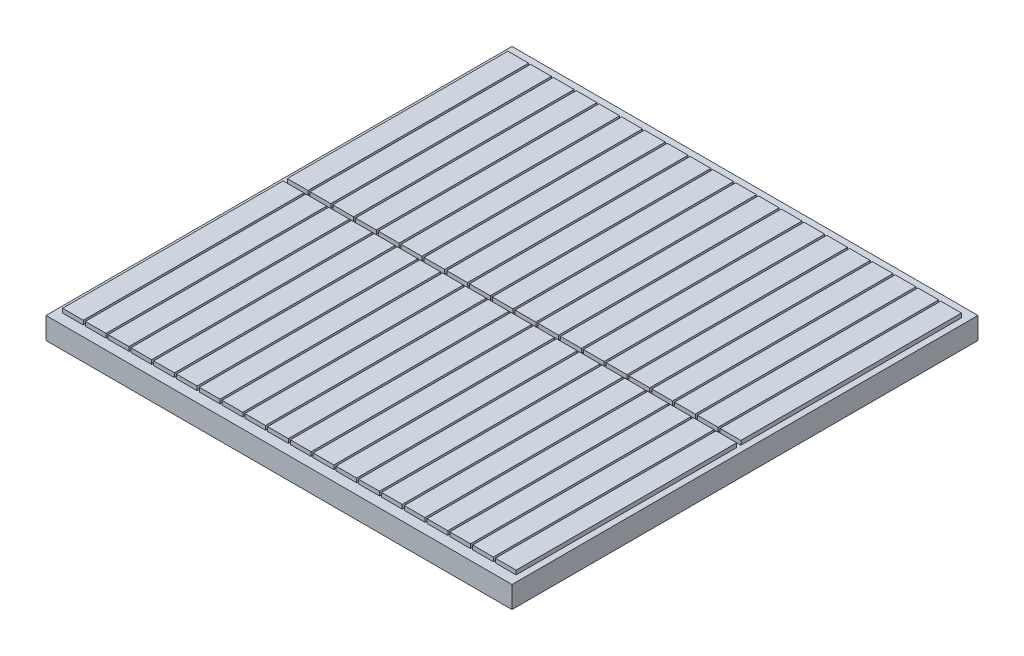
SolidWorks part; units mm, degrees
ref_plane "Front Plane" through (0, 0, 0) normal (0, 0, 1) x (1, 0, 0)
ref_plane "Top Plane" through (0, 0, 0) normal (0, 1, 0) x (1, 0, 0)
ref_plane "Right Plane" through (0, 0, 0) normal (1, 0, 0) x (0, 0, -1)
sketch "Sketch1" plane through (0, 0, 0) normal (0, 1, 0) x (1, 0, 0)
  line L5 (-22.5, 22.5) -> (22.5, 22.5)
  line L6 (-22.5, 22.5) -> (-22.5, -22.5)
  line L7 (-22.5, -22.5) -> (22.5, -22.5)
  line L8 (22.5, 22.5) -> (22.5, -22.5)
  line L9 (-22.5, 22.5) -> (22.5, -22.5) construction
  line L10 (-22.5, -22.5) -> (22.5, 22.5) construction
  point P0 (0, 0)
  point P1 (0, 0)
  dimension "D1" = 45
  dimension "D2" = 45
extrude "Boss-Extrude1" add sketch "Sketch1" along normal blind 0.1
sketch "Sketch2" plane through (0, 0.1, 0) normal (0, 1, 0) x (1, 0, 0)
  line L1 (-22.5, 22.5) -> (22.5, 22.5)
  line L2 (-22.5, 22.5) -> (-22.5, -22.5)
  line L3 (-22.5, -22.5) -> (22.5, -22.5)
  line L4 (22.5, 22.5) -> (22.5, -22.5)
  line L5 (-22.5, 22.5) -> (22.5, -22.5) construction
  line L6 (-22.5, -22.5) -> (22.5, 22.5) construction
  point P0 (0, 0)
  dimension "D1" = 45
  dimension "D2" = 45
extrude "Boss-Extrude2" add sketch "Sketch2" along normal blind 2
sketch "Sketch5" plane through (0, 2.1, 0) normal (0, 1, 0) x (1, 0, 0)
  line L0 (22.5, 22.5) -> (-22.5, 22.5) construction
  line L1 (-21.9, 21.5) -> (-19.9, 21.5)
  line L2 (-21.9, 21.5) -> (-21.9, 0.2)
  line L3 (-21.9, 0.2) -> (-19.9, 0.2)
  line L4 (-19.9, 21.5) -> (-19.9, 0.2)
  line L5 (-22.5, 22.5) -> (-22.5, -22.5) construction
  line L6 (-19.7, 21.5) -> (-19.7, 0.2)
  line L7 (-19.7, 21.5) -> (-17.7, 21.5)
  line L56 (-21.9, 21.5) -> (-19.7, 21.5) construction
  line L57 (-17.7, 21.5) -> (-17.7, 0.2)
  line L110 (-19.7, 0.2) -> (-17.7, 0.2)
  line L111 (-17.5, 21.5) -> (-17.5, 0.2)
  line L112 (-17.5, 21.5) -> (-15.5, 21.5)
  line L113 (-15.5, 21.5) -> (-15.5, 0.2)
  line L114 (-17.5, 0.2) -> (-15.5, 0.2)
  line L115 (-15.3, 21.5) -> (-15.3, 0.2)
  line L116 (-15.3, 21.5) -> (-13.3, 21.5)
  line L117 (-13.3, 21.5) -> (-13.3, 0.2)
  line L118 (-15.3, 0.2) -> (-13.3, 0.2)
  line L119 (-13.1, 21.5) -> (-13.1, 0.2)
  line L120 (-13.1, 21.5) -> (-11.1, 21.5)
  line L121 (-11.1, 21.5) -> (-11.1, 0.2)
  line L122 (-13.1, 0.2) -> (-11.1, 0.2)
  line L123 (-10.9, 21.5) -> (-10.9, 0.2)
  line L124 (-10.9, 21.5) -> (-8.9, 21.5)
  line L125 (-8.9, 21.5) -> (-8.9, 0.2)
  line L126 (-10.9, 0.2) -> (-8.9, 0.2)
  line L127 (-8.7, 21.5) -> (-8.7, 0.2)
  line L128 (-8.7, 21.5) -> (-6.7, 21.5)
  line L129 (-6.7, 21.5) -> (-6.7, 0.2)
  line L130 (-8.7, 0.2) -> (-6.7, 0.2)
  line L131 (-6.5, 21.5) -> (-6.5, 0.2)
  line L132 (-6.5, 21.5) -> (-4.5, 21.5)
  line L133 (-4.5, 21.5) -> (-4.5, 0.2)
  line L134 (-6.5, 0.2) -> (-4.5, 0.2)
  line L135 (-4.3, 21.5) -> (-4.3, 0.2)
  line L136 (-4.3, 21.5) -> (-2.3, 21.5)
  line L137 (-2.3, 21.5) -> (-2.3, 0.2)
  line L138 (-4.3, 0.2) -> (-2.3, 0.2)
  line L139 (-2.1, 21.5) -> (-2.1, 0.2)
  line L140 (-2.1, 21.5) -> (-0.1, 21.5)
  line L141 (-0.1, 21.5) -> (-0.1, 0.2)
  line L142 (-2.1, 0.2) -> (-0.1, 0.2)
  line L143 (0.1, 21.5) -> (0.1, 0.2)
  line L144 (0.1, 21.5) -> (2.1, 21.5)
  line L145 (2.1, 21.5) -> (2.1, 0.2)
  line L146 (0.1, 0.2) -> (2.1, 0.2)
  line L147 (2.3, 21.5) -> (2.3, 0.2)
  line L148 (2.3, 21.5) -> (4.3, 21.5)
  line L149 (4.3, 21.5) -> (4.3, 0.2)
  line L150 (2.3, 0.2) -> (4.3, 0.2)
  line L151 (4.5, 21.5) -> (4.5, 0.2)
  line L152 (4.5, 21.5) -> (6.5, 21.5)
  line L153 (6.5, 21.5) -> (6.5, 0.2)
  line L154 (4.5, 0.2) -> (6.5, 0.2)
  line L155 (6.7, 21.5) -> (6.7, 0.2)
  line L156 (6.7, 21.5) -> (8.7, 21.5)
  line L157 (8.7, 21.5) -> (8.7, 0.2)
  line L158 (6.7, 0.2) -> (8.7, 0.2)
  line L159 (8.9, 21.5) -> (8.9, 0.2)
  line L160 (8.9, 21.5) -> (10.9, 21.5)
  line L161 (10.9, 21.5) -> (10.9, 0.2)
  line L162 (8.9, 0.2) -> (10.9, 0.2)
  line L163 (11.1, 21.5) -> (11.1, 0.2)
  line L164 (11.1, 21.5) -> (13.1, 21.5)
  line L165 (13.1, 21.5) -> (13.1, 0.2)
  line L166 (11.1, 0.2) -> (13.1, 0.2)
  line L167 (13.3, 21.5) -> (13.3, 0.2)
  line L168 (13.3, 21.5) -> (15.3, 21.5)
  line L169 (15.3, 21.5) -> (15.3, 0.2)
  line L170 (13.3, 0.2) -> (15.3, 0.2)
  line L171 (15.5, 21.5) -> (15.5, 0.2)
  line L172 (15.5, 21.5) -> (17.5, 21.5)
  line L173 (17.5, 21.5) -> (17.5, 0.2)
  line L174 (15.5, 0.2) -> (17.5, 0.2)
  line L175 (17.7, 21.5) -> (17.7, 0.2)
  line L176 (17.7, 21.5) -> (19.7, 21.5)
  line L177 (19.7, 21.5) -> (19.7, 0.2)
  line L178 (17.7, 0.2) -> (19.7, 0.2)
  line L179 (19.9, 21.5) -> (19.9, 0.2)
  line L180 (19.9, 21.5) -> (21.9, 21.5)
  line L181 (21.9, 21.5) -> (21.9, 0.2)
  line L182 (19.9, 0.2) -> (21.9, 0.2)
  line L184 (0, 0) -> (0.7148, 0)
  line L185 (-17.5, -21.5) -> (-15.5, -21.5)
  line L186 (-19.7, -21.5) -> (-17.7, -21.5)
  line L187 (-21.9, -21.5) -> (-19.9, -21.5)
  line L188 (-15.3, -21.5) -> (-13.3, -21.5)
  line L189 (-13.1, -21.5) -> (-11.1, -21.5)
  line L190 (2.3, -21.5) -> (4.3, -21.5)
  line L191 (0.1, -21.5) -> (2.1, -21.5)
  line L192 (-2.1, -21.5) -> (-0.1, -21.5)
  line L193 (-4.3, -21.5) -> (-2.3, -21.5)
  line L194 (-6.5, -21.5) -> (-4.5, -21.5)
  line L195 (-8.7, -21.5) -> (-6.7, -21.5)
  line L196 (-10.9, -21.5) -> (-8.9, -21.5)
  line L197 (4.5, -21.5) -> (6.5, -21.5)
  line L198 (6.7, -21.5) -> (8.7, -21.5)
  line L199 (8.9, -21.5) -> (10.9, -21.5)
  line L200 (11.1, -21.5) -> (13.1, -21.5)
  line L201 (15.5, -21.5) -> (17.5, -21.5)
  line L202 (13.3, -21.5) -> (15.3, -21.5)
  line L203 (19.9, -21.5) -> (21.9, -21.5)
  line L204 (17.7, -21.5) -> (19.7, -21.5)
  line L205 (19.9, -0.2) -> (21.9, -0.2)
  line L206 (17.7, -0.2) -> (19.7, -0.2)
  line L207 (15.5, -0.2) -> (17.5, -0.2)
  line L208 (13.3, -0.2) -> (15.3, -0.2)
  line L209 (11.1, -0.2) -> (13.1, -0.2)
  line L210 (10.9, -21.5) -> (10.9, -0.2)
  line L211 (11.1, -21.5) -> (11.1, -0.2)
  line L212 (13.3, -21.5) -> (13.3, -0.2)
  line L213 (13.1, -21.5) -> (13.1, -0.2)
  line L214 (15.3, -21.5) -> (15.3, -0.2)
  line L215 (15.5, -21.5) -> (15.5, -0.2)
  line L216 (17.5, -21.5) -> (17.5, -0.2)
  line L217 (17.7, -21.5) -> (17.7, -0.2)
  line L218 (19.7, -21.5) -> (19.7, -0.2)
  line L219 (19.9, -21.5) -> (19.9, -0.2)
  line L220 (21.9, -21.5) -> (21.9, -0.2)
  line L221 (8.7, -21.5) -> (8.7, -0.2)
  line L222 (8.9, -21.5) -> (8.9, -0.2)
  line L223 (8.9, -0.2) -> (10.9, -0.2)
  line L224 (6.7, -0.2) -> (8.7, -0.2)
  line L225 (4.5, -0.2) -> (6.5, -0.2)
  line L226 (2.3, -0.2) -> (4.3, -0.2)
  line L227 (0.1, -0.2) -> (2.1, -0.2)
  line L228 (-2.1, -0.2) -> (-0.1, -0.2)
  line L229 (-2.3, -21.5) -> (-2.3, -0.2)
  line L230 (-2.1, -21.5) -> (-2.1, -0.2)
  line L231 (-0.1, -21.5) -> (-0.1, -0.2)
  line L232 (0.1, -21.5) -> (0.1, -0.2)
  line L233 (2.1, -21.5) -> (2.1, -0.2)
  line L234 (2.3, -21.5) -> (2.3, -0.2)
  line L235 (4.3, -21.5) -> (4.3, -0.2)
  line L236 (4.5, -21.5) -> (4.5, -0.2)
  line L237 (6.5, -21.5) -> (6.5, -0.2)
  line L238 (6.7, -21.5) -> (6.7, -0.2)
  line L239 (-4.3, -0.2) -> (-2.3, -0.2)
  line L240 (-4.3, -21.5) -> (-4.3, -0.2)
  line L241 (-4.5, -21.5) -> (-4.5, -0.2)
  line L242 (-6.5, -0.2) -> (-4.5, -0.2)
  line L243 (-6.5, -21.5) -> (-6.5, -0.2)
  line L244 (-6.7, -21.5) -> (-6.7, -0.2)
  line L245 (-8.7, -21.5) -> (-8.7, -0.2)
  line L246 (-8.9, -21.5) -> (-8.9, -0.2)
  line L247 (-17.7, -21.5) -> (-17.7, -0.2)
  line L248 (-17.5, -21.5) -> (-17.5, -0.2)
  line L249 (-15.5, -21.5) -> (-15.5, -0.2)
  line L250 (-15.3, -21.5) -> (-15.3, -0.2)
  line L251 (-13.1, -21.5) -> (-13.1, -0.2)
  line L252 (-13.3, -21.5) -> (-13.3, -0.2)
  line L253 (-10.9, -21.5) -> (-10.9, -0.2)
  line L254 (-11.1, -21.5) -> (-11.1, -0.2)
  line L255 (-8.7, -0.2) -> (-6.7, -0.2)
  line L256 (-10.9, -0.2) -> (-8.9, -0.2)
  line L257 (-13.1, -0.2) -> (-11.1, -0.2)
  line L258 (-15.3, -0.2) -> (-13.3, -0.2)
  line L259 (-17.5, -0.2) -> (-15.5, -0.2)
  line L260 (-19.7, -0.2) -> (-17.7, -0.2)
  line L261 (-19.7, -21.5) -> (-19.7, -0.2)
  line L262 (-19.9, -21.5) -> (-19.9, -0.2)
  line L263 (-21.9, -0.2) -> (-19.9, -0.2)
  line L264 (-21.9, -21.5) -> (-21.9, -0.2)
  dimension "D1" = 1
  dimension "D2" = 0.6
  dimension "D3" = 2
  dimension "D4" = 20
extrude "Boss-Extrude3" add sketch "Sketch5" along normal blind 0.4 contours L4 L1 L2 L3 | L6 L110 L57 L7 | L111 L114 L113 L112 | L115 L118 L117 L116 | L119 L122 L121 L120 | L123 L126 L125 L124 | L127 L130 L129 L128 | L131 L134 L133 L132 | L135 L138 L137 L136 | L139 L142 L141 L140 | L143 L146 L145 L144 | L147 L150 L149 L148 | L155 L158 L157 L156 | L159 L162 L161 L160 | L163 L166 L165 L164 | L167 L170 L169 L168 | L171 L174 L173 L172 | L175 L178 L177 L176 | L179 L182 L181 L180 | L203 L220 L205 L219 | L202 L214 L208 L212 | L200 L213 L209 L211 | L223 L222 L199 L210 | L238 L198 L221 L224 | L197 L237 L225 L236 | L191 L233 L227 L232 | L192 L231 L228 L230 | L240 L193 L229 L239 | L243 L194 L241 L242 | L255 L245 L195 L244 | L256 L253 L196 L246 | L257 L251 L189 L254 | L258 L250 L188 L252 | L259 L248 L185 L249 | L261 L186 L247 L260 | L264 L187 L262 L263 | L151 L154 L153 L152 | L218 L206 L217 L204 | L215 L207 L216 L201 | L235 L226 L234 L190
